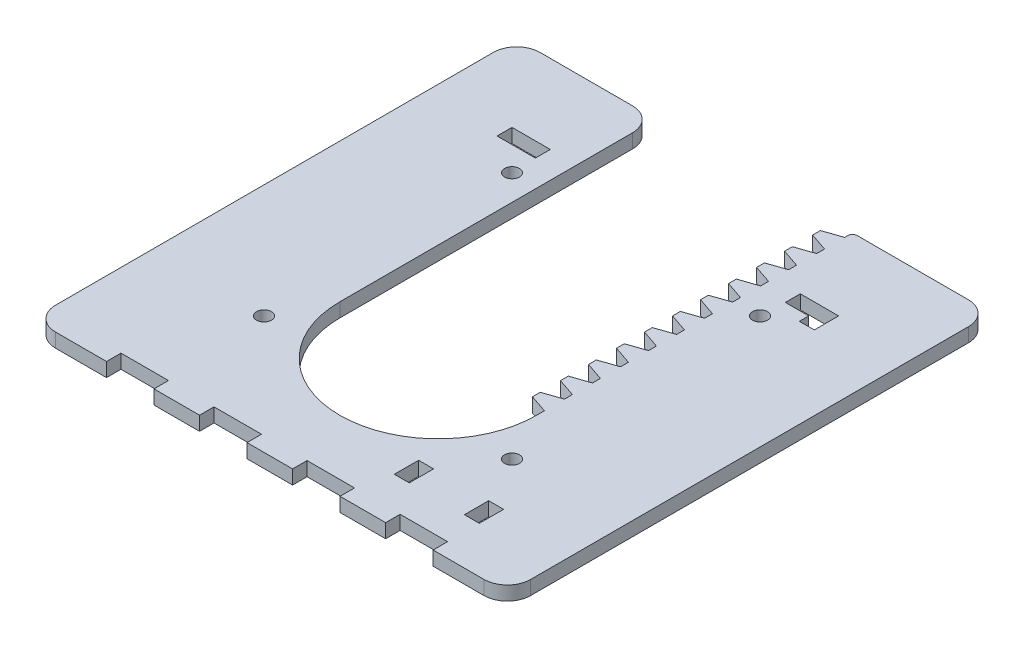
SolidWorks part; units mm, degrees
ref_plane "Front Plane" through (0, 0, 0) normal (0, 0, 1) x (1, 0, 0)
ref_plane "Top Plane" through (0, 0, 0) normal (0, 1, 0) x (1, 0, 0)
ref_plane "Right Plane" through (0, 0, 0) normal (1, 0, 0) x (0, 0, -1)
sketch "Sketch1" plane through (0, 0, 0) normal (0, 1, 0) x (1, 0, 0)
  line L0 (0, 0) -> (0, 21) construction
  line L1 (17.1887, 0) -> (0, 0) construction
  line L2 (21.0585, 3.843) -> (17.1887, 5.1665) construction
  line L3 (17.1887, 5.1665) -> (17.1887, 6.8335) construction
  line L4 (17.1887, 6.8335) -> (21.0585, 8.157) construction
  line L5 (21.0585, 9.843) -> (21.0585, 8.157) construction
  line L6 (21.0585, 9.843) -> (17.1887, 11.1665) construction
  line L7 (17.1887, 11.1665) -> (17.1887, 12.8335) construction
  line L8 (17.1887, 12.8335) -> (21.0585, 14.157) construction
  line L9 (21.0585, 15.843) -> (21.0585, 14.157) construction
  line L10 (21.0585, 15.843) -> (17.1887, 17.1665) construction
  line L11 (17.1887, 17.1665) -> (17.1887, 18.8335) construction
  line L12 (17.1887, 18.8335) -> (21.0585, 20.157) construction
  line L13 (21.0585, 21.843) -> (21.0585, 20.157) construction
  line L14 (21.0585, 21.843) -> (17.1887, 23.1665) construction
  line L15 (17.1887, 23.1665) -> (17.1887, 24.8335) construction
  line L16 (17.1887, 24.8335) -> (21.0585, 26.157) construction
  line L17 (21.0585, 27.843) -> (21.0585, 26.157) construction
  line L18 (21.0585, 27.843) -> (17.1887, 29.1665) construction
  line L19 (17.1887, 29.1665) -> (17.1887, 30.8335) construction
  line L20 (17.1887, 30.8335) -> (21.0585, 32.157) construction
  line L21 (21.0585, 33.843) -> (21.0585, 32.157) construction
  line L22 (21.0585, 33.843) -> (17.1887, 35.1665) construction
  line L23 (17.1887, 35.1665) -> (17.1887, 36.8335) construction
  line L24 (17.1887, 36.8335) -> (21.0585, 38.157) construction
  line L25 (21.0585, 39.843) -> (21.0585, 38.157) construction
  line L26 (21.0585, 39.843) -> (17.1887, 41.1665) construction
  line L27 (17.1887, 41.1665) -> (17.1887, 42.8335) construction
  line L28 (17.1887, 42.8335) -> (21.0585, 44.157) construction
  line L29 (21.0585, 45.843) -> (21.0585, 44.157) construction
  line L30 (21.0585, 45.843) -> (17.1887, 47.1665) construction
  line L31 (17.1887, 47.1665) -> (17.1887, 48.8335) construction
  line L32 (17.1887, 48.8335) -> (21.0585, 50.157) construction
  line L33 (21.0585, 51.843) -> (21.0585, 50.157) construction
  line L34 (21.0585, 51.843) -> (17.1887, 53.1665) construction
  line L35 (17.1887, 53.1665) -> (17.1887, 54.8335) construction
  line L36 (17.1887, 54.8335) -> (21.0585, 56.157) construction
  line L37 (21.0585, 57.843) -> (21.0585, 56.157) construction
  line L38 (21.0585, 57.843) -> (17.1887, 59.1665) construction
  line L39 (17.1887, 59.1665) -> (17.1887, 60.8335) construction
  line L40 (17.1887, 60.8335) -> (21.0585, 62.157) construction
  line L41 (21.0585, 62.157) -> (21.0585, 62.843) construction
  line L42 (45.8722, 63.843) -> (22.0585, 63.843) construction
  line L43 (50.8722, -34.9014) -> (50.8722, 58.843) construction
  line L44 (45.8722, -39.9014) -> (-45.8722, -39.9014) construction
  line L45 (-50.8722, 58.843) -> (-50.8722, -34.9014) construction
  line L46 (-45.8722, 63.843) -> (-22.0585, 63.843) construction
  line L47 (-21.0585, -3.843) -> (-21.0585, 62.843) construction
  line L48 (21.0585, -2.157) -> (21.0585, -3.843) construction
  line L49 (21.0585, -2.157) -> (17.1887, -0.8335) construction
  line L50 (17.1887, -0.8335) -> (17.1887, 0.8335) construction
  line L51 (17.1887, 0.8335) -> (21.0585, 2.157) construction
  line L52 (21.0585, 3.843) -> (21.0585, 2.157) construction
  line L53 (21.0585, 3.843) -> (17.1887, 5.1665)
  line L54 (17.1887, 5.1665) -> (17.1887, 6.8335)
  line L55 (17.1887, 6.8335) -> (21.0585, 8.157)
  line L56 (21.0585, 9.843) -> (21.0585, 8.157)
  line L57 (21.0585, 9.843) -> (17.1887, 11.1665)
  line L58 (17.1887, 11.1665) -> (17.1887, 12.8335)
  line L59 (17.1887, 12.8335) -> (21.0585, 14.157)
  line L60 (21.0585, 15.843) -> (21.0585, 14.157)
  line L61 (21.0585, 15.843) -> (17.1887, 17.1665)
  line L62 (17.1887, 17.1665) -> (17.1887, 18.8335)
  line L63 (17.1887, 18.8335) -> (21.0585, 20.157)
  line L64 (21.0585, 21.843) -> (21.0585, 20.157)
  line L65 (21.0585, 21.843) -> (17.1887, 23.1665)
  line L66 (17.1887, 23.1665) -> (17.1887, 24.8335)
  line L67 (17.1887, 24.8335) -> (21.0585, 26.157)
  line L68 (21.0585, 27.843) -> (21.0585, 26.157)
  line L69 (21.0585, 27.843) -> (17.1887, 29.1665)
  line L70 (17.1887, 29.1665) -> (17.1887, 30.8335)
  line L71 (17.1887, 30.8335) -> (21.0585, 32.157)
  line L72 (21.0585, 33.843) -> (21.0585, 32.157)
  line L73 (21.0585, 33.843) -> (17.1887, 35.1665)
  line L74 (17.1887, 35.1665) -> (17.1887, 36.8335)
  line L75 (17.1887, 36.8335) -> (21.0585, 38.157)
  line L76 (21.0585, 39.843) -> (21.0585, 38.157)
  line L77 (21.0585, 39.843) -> (17.1887, 41.1665)
  line L78 (17.1887, 41.1665) -> (17.1887, 42.8335)
  line L79 (17.1887, 42.8335) -> (21.0585, 44.157)
  line L80 (21.0585, 45.843) -> (21.0585, 44.157)
  line L81 (21.0585, 45.843) -> (17.1887, 47.1665)
  line L82 (17.1887, 47.1665) -> (17.1887, 48.8335)
  line L83 (17.1887, 48.8335) -> (21.0585, 50.157)
  line L84 (21.0585, 51.843) -> (21.0585, 50.157)
  line L85 (21.0585, 51.843) -> (17.1887, 53.1665)
  line L86 (17.1887, 53.1665) -> (17.1887, 54.8335)
  line L87 (17.1887, 54.8335) -> (21.0585, 56.157)
  line L88 (21.0585, 57.843) -> (21.0585, 56.157)
  line L89 (21.0585, 57.843) -> (17.1887, 59.1665)
  line L90 (17.1887, 59.1665) -> (17.1887, 60.8335)
  line L91 (17.1887, 60.8335) -> (21.0585, 62.157)
  line L92 (21.0585, 62.157) -> (21.0585, 62.843)
  line L93 (45.8722, 63.843) -> (22.0585, 63.843)
  line L94 (50.8722, -34.9014) -> (50.8722, 58.843)
  line L95 (45.8722, -39.9014) -> (-45.8722, -39.9014)
  line L96 (-50.8722, 58.843) -> (-50.8722, -34.9014)
  line L97 (-45.8722, 63.843) -> (-26.0585, 63.843)
  line L98 (-21.0585, -3.843) -> (-21.0585, 58.843)
  line L99 (21.0585, -2.157) -> (21.0585, -3.843)
  line L100 (21.0585, -2.157) -> (17.1887, -0.8335)
  line L101 (17.1887, -0.8335) -> (17.1887, 0.8335)
  line L102 (17.1887, 0.8335) -> (21.0585, 2.157)
  line L103 (21.0585, 3.843) -> (21.0585, 2.157)
  line L104 (0, 63.843) -> (0, -39.9014) construction
  line L105 (-51.8722, 11.9708) -> (51.8722, 11.9708) construction
  line L106 (0, 11.9708) -> (-51.8722, -39.9014) construction
  line L107 (51.8722, -24.9014) -> (-51.8722, -24.9014) construction
  line L108 (-36.8722, -39.9014) -> (-36.8722, 63.843) construction
  line L109 (36.8722, -39.9014) -> (36.8722, 63.843) construction
  line L110 (45.8722, -39.9014) -> (51.8722, -39.9014) construction
  line L111 (51.8722, -39.9014) -> (51.8722, 63.843) construction
  line L112 (51.8722, 63.843) -> (-51.8722, 63.843) construction
  line L113 (17.1887, 60) -> (0, 60) construction
  line L114 (-51.8722, 63.843) -> (-51.8722, -39.9014) construction
  line L115 (-51.8722, -39.9014) -> (-45.8722, -39.9014) construction
  circle A0 centre (0, 0) radius 21 construction
  circle A1 centre (0, 60) radius 21 construction
  arc A2 (22.0585, 63.843) -> (21.0585, 62.843) centre (22.0585, 62.843) ccw construction
  arc A3 (50.8722, 58.843) -> (45.8722, 63.843) centre (45.8722, 58.843) ccw construction
  arc A4 (45.8722, -39.9014) -> (50.8722, -34.9014) centre (45.8722, -34.9014) ccw construction
  arc A5 (-50.8722, -34.9014) -> (-45.8722, -39.9014) centre (-45.8722, -34.9014) ccw construction
  arc A6 (-45.8722, 63.843) -> (-50.8722, 58.843) centre (-45.8722, 58.843) ccw construction
  arc A8 (-21.0585, -3.843) -> (21.0585, -3.843) centre (0, -3.843) ccw construction
  arc A9 (22.0585, 63.843) -> (21.0585, 62.843) centre (22.0585, 62.843) ccw
  arc A10 (50.8722, 58.843) -> (45.8722, 63.843) centre (45.8722, 58.843) ccw
  arc A11 (45.8722, -39.9014) -> (50.8722, -34.9014) centre (45.8722, -34.9014) ccw
  arc A12 (-50.8722, -34.9014) -> (-45.8722, -39.9014) centre (-45.8722, -34.9014) ccw
  arc A13 (-45.8722, 63.843) -> (-50.8722, 58.843) centre (-45.8722, 58.843) ccw
  arc A14 (-21.0585, 58.843) -> (-26.0585, 63.843) centre (-26.0585, 58.843) ccw
  arc A15 (-21.0585, -3.843) -> (21.0585, -3.843) centre (0, -3.843) ccw
  circle A16 centre (26.5585, -14.5877) radius 1.6 construction
  circle A17 centre (-26.5585, -14.5877) radius 1.6 construction
  circle A18 centre (-26.5585, 38.5292) radius 1.6 construction
  circle A19 centre (26.5585, 38.5292) radius 1.6 construction
  circle A20 centre (26.5585, -14.5877) radius 1.6
  circle A21 centre (-26.5585, -14.5877) radius 1.6
  circle A22 centre (-26.5585, 38.5292) radius 1.6
  circle A23 centre (26.5585, 38.5292) radius 1.6
  circle A24 centre (0, 60) radius 21 construction
sketch "Sketch2" plane through (0, 0, 0) normal (0, 0, 1) x (1, 0, 0)
  line L0 (0, 0) -> (0, 3) construction
  line L1 (-50.8722, 0) -> (50.8722, 0)
  line L2 (-50.8722, 0) -> (-50.8722, 3)
  line L3 (-50.8722, 3) -> (50.8722, 3)
  line L4 (50.8722, 0) -> (50.8722, 3)
  line L5 (-50.8722, 3) -> (-51.8722, 3) construction
  line L6 (-51.8722, 3) -> (-51.8722, 3.75) construction
  line L7 (-51.8722, 3.75) -> (51.8722, 3.75) construction
  line L8 (51.8722, 3.75) -> (51.8722, 3) construction
  line L9 (51.8722, 3) -> (50.8722, 3) construction
  line L10 (50.8722, 0) -> (51.8722, 0) construction
  line L11 (51.8722, 0) -> (51.8722, -0.75) construction
  line L12 (51.8722, -0.75) -> (-51.8722, -0.75) construction
  line L13 (-51.8722, -0.75) -> (-51.8722, 0) construction
  line L14 (-51.8722, 0) -> (-50.8722, 0) construction
  line L15 (59.7, 47.7) -> (59.7, 44.7) construction
  dimension "D2" = 0.75
extrude "Boss-Extrude1" add sketch "Sketch1" along normal up to vertex (3 mm away) up to point (-50.8722, 3, 0)
ref_plane "edge" through (0, 0, -63.843) normal (0, 0, 1) x (1, 0, 0)
sketch "Sketch4" plane through (0, 0, 0) normal (0, 1, 0) x (1, 0, 0)
  line L12 (-25.0418, -23.0877) -> (-25.0418, -20.0877) construction
  line L13 (-15.0251, -23.0877) -> (-15.0251, -20.0877) construction
  line L14 (-5.0084, -23.0877) -> (-5.0084, -20.0877) construction
  line L15 (5.0084, -23.0877) -> (5.0084, -20.0877) construction
  line L16 (15.0251, -23.0877) -> (15.0251, -20.0877) construction
  line L17 (25.0418, -20.0877) -> (25.0418, -23.0877) construction
  line L18 (32.0585, -20.0877) -> (35.0585, -20.0877) construction
  line L30 (-25.0418, -23.0877) -> (-25.0418, -20.0877)
  line L31 (-15.0251, -23.0877) -> (-15.0251, -20.0877)
  line L32 (-5.0084, -23.0877) -> (-5.0084, -20.0877)
  line L33 (5.0084, -23.0877) -> (5.0084, -20.0877)
  line L34 (15.0251, -23.0877) -> (15.0251, -20.0877)
  line L35 (25.0418, -20.0877) -> (25.0418, -23.0877)
  line L36 (-35.0585, 47.0292) -> (35.0585, 47.0292) construction
  line L37 (-32.0585, 44.0292) -> (32.0585, 44.0292) construction
  line L38 (-32.0585, -20.0877) -> (-32.0585, 44.0292) construction
  line L39 (-35.0585, -23.0877) -> (-35.0585, 47.0292) construction
  line L40 (-32.0585, -20.0877) -> (32.0585, -20.0877) construction
  line L41 (-35.0585, -23.0877) -> (35.0585, -23.0877) construction
  line L42 (32.0585, -20.0877) -> (32.0585, 44.0292) construction
  line L43 (35.0585, -23.0877) -> (35.0585, 47.0292) construction
  line L44 (-35.0585, 47.0292) -> (35.0585, 47.0292)
  line L45 (-32.0585, 44.0292) -> (32.0585, 44.0292)
  line L46 (-32.0585, -20.0877) -> (-32.0585, 44.0292)
  line L47 (-35.0585, -23.0877) -> (-35.0585, 47.0292)
  line L48 (-32.0585, -20.0877) -> (32.0585, -20.0877)
  line L49 (-35.0585, -23.0877) -> (35.0585, -23.0877)
  line L50 (32.0585, -20.0877) -> (32.0585, 44.0292)
  line L51 (35.0585, -23.0877) -> (35.0585, 47.0292)
  line L52 (-23.0585, 44.0292) -> (-23.0585, 47.0292) construction
  line L53 (-23.0585, 44.0292) -> (-23.0585, 47.0292)
  line L54 (23.0585, 44.0292) -> (23.0585, 47.0292) construction
  line L55 (23.0585, 44.0292) -> (23.0585, 47.0292)
  line L56 (-32.0585, 44.0292) -> (-35.0585, 44.0292) construction
  line L57 (-25.0418, 47.0292) -> (-25.0418, 44.0292) construction
  line L58 (25.0418, 47.0292) -> (25.0418, 44.0292) construction
  line L59 (32.0585, 47.0292) -> (32.0585, 44.0292) construction
  line L66 (-32.0585, -20.0877) -> (-32.0585, -23.0877) construction
sketch "Sketch3" plane through (0, 0, 0) normal (0, 1, 0) x (1, 0, 0)
  line L0 (32.0585, 37.0125) -> (35.0585, 37.0125) construction
  line L1 (25.0418, 47.0292) -> (25.0418, 44.0292) construction
  line L2 (25.0418, 44.0292) -> (32.0585, 44.0292) construction
  line L3 (32.0585, 44.0292) -> (32.0585, 37.0125) construction
  line L4 (32.0585, 37.0125) -> (35.0585, 37.0125) construction
  line L5 (35.0585, 37.0125) -> (35.0585, 47.0292) construction
  line L6 (35.0585, 47.0292) -> (25.0418, 47.0292) construction
  line L7 (35.0585, -23.0877) -> (35.0585, 47.0292) construction
  line L8 (32.0585, 11.9708) -> (0, 11.9708) construction
  line L9 (0, 11.9708) -> (0, 44.0292) construction
  line L10 (32.0585, 11.9708) -> (0, 11.9708) construction
  line L11 (0, 11.9708) -> (0, 44.0292) construction
  line L13 (35.0585, 26.9958) -> (32.0585, 26.9958) construction
  line L14 (35.0585, 16.9791) -> (32.0585, 16.9791) construction
  line L15 (32.0585, -20.0877) -> (32.0585, 44.0292) construction
  line L16 (35.0585, 26.9958) -> (32.0585, 26.9958) construction
  line L17 (35.0585, 26.9958) -> (35.0585, 16.9791) construction
  line L18 (35.0585, 16.9791) -> (32.0585, 16.9791) construction
  line L19 (32.0585, 26.9958) -> (32.0585, 16.9791) construction
  line L20 (35.1585, 27.0958) -> (35.1585, 16.8791)
  line L21 (35.1585, 16.8791) -> (31.9585, 16.8791)
  line L22 (31.9585, 27.0958) -> (31.9585, 16.8791)
  line L23 (35.1585, 27.0958) -> (31.9585, 27.0958)
  line L24 (35.1585, 36.9125) -> (35.1585, 47.1292)
  line L25 (35.1585, 47.1292) -> (24.9418, 47.1292)
  line L26 (24.9418, 47.1292) -> (24.9418, 43.9292)
  line L27 (24.9418, 43.9292) -> (31.9585, 43.9292)
  line L28 (31.9585, 43.9292) -> (31.9585, 36.9125)
  line L29 (31.9585, 36.9125) -> (35.1585, 36.9125)
  line L30 (35.1585, -3.1543) -> (31.9585, -3.1543)
  line L31 (31.9585, -3.1543) -> (31.9585, 7.0624)
  line L32 (35.1585, 7.0624) -> (31.9585, 7.0624)
  line L33 (35.1585, -3.1543) -> (35.1585, 7.0624)
  line L34 (31.9585, -19.9877) -> (31.9585, -12.971)
  line L35 (24.9418, -19.9877) -> (31.9585, -19.9877)
  line L36 (24.9418, -23.1877) -> (24.9418, -19.9877)
  line L37 (35.1585, -23.1877) -> (24.9418, -23.1877)
  line L38 (35.1585, -12.971) -> (35.1585, -23.1877)
  line L39 (31.9585, -12.971) -> (35.1585, -12.971)
  line L40 (-31.9585, 43.9292) -> (-31.9585, 36.9125)
  line L41 (-24.9418, 43.9292) -> (-31.9585, 43.9292)
  line L42 (-24.9418, 47.1292) -> (-24.9418, 43.9292)
  line L43 (-35.1585, 47.1292) -> (-24.9418, 47.1292)
  line L44 (-35.1585, 36.9125) -> (-35.1585, 47.1292)
  line L45 (-31.9585, 36.9125) -> (-35.1585, 36.9125)
  line L46 (-35.1585, 27.0958) -> (-35.1585, 16.8791)
  line L47 (-35.1585, 16.8791) -> (-31.9585, 16.8791)
  line L48 (-31.9585, 27.0958) -> (-31.9585, 16.8791)
  line L49 (-35.1585, 27.0958) -> (-31.9585, 27.0958)
  line L50 (-35.1585, -3.1543) -> (-31.9585, -3.1543)
  line L51 (-31.9585, -3.1543) -> (-31.9585, 7.0624)
  line L52 (-35.1585, 7.0624) -> (-31.9585, 7.0624)
  line L53 (-35.1585, -3.1543) -> (-35.1585, 7.0624)
  line L54 (-35.1585, -12.971) -> (-35.1585, -23.1877)
  line L55 (-31.9585, -12.971) -> (-35.1585, -12.971)
  line L56 (-31.9585, -19.9877) -> (-31.9585, -12.971)
  line L57 (-24.9418, -19.9877) -> (-31.9585, -19.9877)
  line L58 (-24.9418, -23.1877) -> (-24.9418, -19.9877)
  line L59 (-35.1585, -23.1877) -> (-24.9418, -23.1877)
  dimension "D1" = 0.1
extrude "Cut-Extrude1" [suppressed] cut sketch "Sketch3" along normal through all
sketch "Sketch6" plane through (0, 0, 0) normal (0, 1, 0) x (1, 0, 0)
  line L0 (34.8722, -39.9014) -> (34.8722, 63.843) construction
  line L1 (31.8722, -39.9014) -> (31.8722, 63.843) construction
  line L2 (24.9087, -39.9014) -> (24.9087, 63.843) construction
  line L3 (-24.9087, -39.9014) -> (-24.9087, 63.843) construction
  line L4 (14.9452, -39.9014) -> (14.9452, -36.9014)
  line L5 (14.9452, -36.9014) -> (4.9817, -36.9014)
  line L6 (4.9817, -36.9014) -> (4.9817, -39.9014)
  line L7 (4.9817, -39.9014) -> (14.9452, -39.9014)
  line L8 (14.9452, -39.9014) -> (14.9452, -36.9014) construction
  line L9 (14.9452, -36.9014) -> (4.9817, -36.9014) construction
  line L10 (4.9817, -36.9014) -> (4.9817, -39.9014) construction
  line L11 (4.9817, -39.9014) -> (14.9452, -39.9014) construction
  line L12 (34.8722, -36.9014) -> (24.9087, -36.9014)
  line L13 (34.8722, -39.9014) -> (34.8722, -36.9014)
  line L14 (24.9087, -39.9014) -> (34.8722, -39.9014)
  line L15 (24.9087, -36.9014) -> (24.9087, -39.9014)
  line L16 (34.8722, -36.9014) -> (24.9087, -36.9014) construction
  line L17 (34.8722, -39.9014) -> (34.8722, -36.9014) construction
  line L18 (24.9087, -39.9014) -> (34.8722, -39.9014) construction
  line L19 (24.9087, -36.9014) -> (24.9087, -39.9014) construction
  line L20 (-24.9087, -36.9014) -> (-34.8722, -36.9014)
  line L21 (-24.9087, -39.9014) -> (-24.9087, -36.9014)
  line L22 (-34.8722, -39.9014) -> (-24.9087, -39.9014)
  line L23 (-34.8722, -36.9014) -> (-34.8722, -39.9014)
  line L24 (-24.9087, -36.9014) -> (-34.8722, -36.9014) construction
  line L25 (-24.9087, -39.9014) -> (-24.9087, -36.9014) construction
  line L26 (16.8722, -39.9014) -> (16.8722, 63.843) construction
  line L27 (-34.8722, -39.9014) -> (-24.9087, -39.9014) construction
  line L28 (51.8722, 63.843) -> (51.8722, -39.9014) construction
  line L29 (-34.8722, -36.9014) -> (-34.8722, -39.9014) construction
  line L30 (-14.9452, -39.9014) -> (-4.9817, -39.9014)
  line L31 (-14.9452, -36.9014) -> (-14.9452, -39.9014)
  line L32 (-4.9817, -36.9014) -> (-14.9452, -36.9014)
  line L33 (51.8722, -39.9014) -> (-51.8722, -39.9014) construction
  line L34 (51.8722, 63.843) -> (-51.8722, 63.843) construction
  line L35 (-51.8722, 63.843) -> (-51.8722, -39.9014) construction
  line L36 (51.8722, 63.843) -> (51.8722, -39.9014) construction
  line L37 (51.8722, -39.9014) -> (-51.8722, -39.9014) construction
  line L38 (51.8722, 63.843) -> (-51.8722, 63.843) construction
  line L39 (-51.8722, 63.843) -> (-51.8722, -39.9014) construction
  line L40 (-4.9817, -39.9014) -> (-4.9817, -36.9014)
  line L41 (-14.9452, -39.9014) -> (-4.9817, -39.9014) construction
  line L42 (-14.9452, -36.9014) -> (-14.9452, -39.9014) construction
  line L43 (-4.9817, -36.9014) -> (-14.9452, -36.9014) construction
  line L44 (-4.9817, -39.9014) -> (-4.9817, -36.9014) construction
  line L45 (-34.8722, 43.843) -> (-26.8722, 43.843)
  line L46 (-34.8722, 46.843) -> (-34.8722, 43.843)
  line L47 (-26.8722, 46.843) -> (-34.8722, 46.843)
  line L48 (-26.8722, 43.843) -> (-26.8722, 46.843)
  line L49 (-34.8722, 43.843) -> (-26.8722, 43.843) construction
  line L50 (-34.8722, 46.843) -> (-34.8722, 43.843) construction
  line L51 (-26.8722, 46.843) -> (-34.8722, 46.843) construction
  line L52 (-26.8722, 43.843) -> (-26.8722, 46.843) construction
  line L53 (34.8722, -24.9014) -> (31.8722, -24.9014)
  line L54 (34.8722, -29.9014) -> (34.8722, -24.9014)
  line L55 (31.8722, -29.9014) -> (34.8722, -29.9014)
  line L56 (31.8722, -24.9014) -> (31.8722, -29.9014)
  line L57 (34.8722, -24.9014) -> (31.8722, -24.9014) construction
  line L58 (34.8722, -29.9014) -> (34.8722, -24.9014) construction
  line L59 (31.8722, -29.9014) -> (34.8722, -29.9014) construction
  line L60 (31.8722, -24.9014) -> (31.8722, -29.9014) construction
  line L61 (-34.8722, -39.9014) -> (-34.8722, 63.843) construction
  line L62 (-51.8722, 43.843) -> (51.8722, 43.843) construction
  line L63 (34.8722, 41.843) -> (34.8722, 46.843)
  line L64 (34.8722, 46.843) -> (26.8722, 46.843)
  line L65 (26.8722, 46.843) -> (26.8722, 43.843)
  line L66 (26.8722, 43.843) -> (31.8722, 43.843)
  line L67 (31.8722, 43.843) -> (31.8722, 41.843)
  line L68 (31.8722, 41.843) -> (34.8722, 41.843)
  line L69 (34.8722, 41.843) -> (34.8722, 46.843) construction
  line L70 (34.8722, 46.843) -> (26.8722, 46.843) construction
  line L71 (26.8722, 46.843) -> (26.8722, 43.843) construction
  line L72 (26.8722, 43.843) -> (31.8722, 43.843) construction
  line L73 (31.8722, 43.843) -> (31.8722, 41.843) construction
  line L74 (31.8722, 41.843) -> (34.8722, 41.843) construction
  line L75 (51.8722, 46.843) -> (-51.8722, 46.843) construction
  line L76 (51.8722, -24.9014) -> (-51.8722, -24.9014) construction
  line L77 (51.8722, -36.9014) -> (-51.8722, -36.9014) construction
  line L78 (34.8722, -39.9014) -> (34.8722, 63.843) construction
  line L79 (31.8722, -39.9014) -> (31.8722, 63.843) construction
  line L80 (24.9087, -39.9014) -> (24.9087, 63.843) construction
  line L81 (-24.9087, -39.9014) -> (-24.9087, 63.843) construction
  line L82 (-34.8722, -39.9014) -> (-34.8722, 63.843) construction
  line L83 (-51.8722, 43.843) -> (51.8722, 43.843) construction
  line L84 (51.8722, 46.843) -> (-51.8722, 46.843) construction
  line L85 (51.8722, -24.9014) -> (-51.8722, -24.9014) construction
  line L86 (51.8722, -36.9014) -> (-51.8722, -36.9014) construction
  line L87 (15.0452, -40.0014) -> (15.0452, -36.8014)
  line L88 (15.0452, -36.8014) -> (4.8817, -36.8014)
  line L89 (4.8817, -36.8014) -> (4.8817, -40.0014)
  line L90 (4.8817, -40.0014) -> (15.0452, -40.0014)
  line L91 (34.9722, -36.8014) -> (24.8087, -36.8014)
  line L92 (24.8087, -36.8014) -> (24.8087, -40.0014)
  line L93 (24.8087, -40.0014) -> (34.9722, -40.0014)
  line L94 (34.9722, -40.0014) -> (34.9722, -36.8014)
  line L95 (-24.8087, -36.8014) -> (-34.9722, -36.8014)
  line L96 (-34.9722, -36.8014) -> (-34.9722, -40.0014)
  line L97 (-34.9722, -40.0014) -> (-24.8087, -40.0014)
  line L98 (-24.8087, -40.0014) -> (-24.8087, -36.8014)
  line L99 (-15.0452, -40.0014) -> (-4.8817, -40.0014)
  line L100 (-4.8817, -40.0014) -> (-4.8817, -36.8014)
  line L101 (-4.8817, -36.8014) -> (-15.0452, -36.8014)
  line L102 (-15.0452, -36.8014) -> (-15.0452, -40.0014)
  line L103 (-34.9722, 43.743) -> (-26.7722, 43.743)
  line L104 (-26.7722, 43.743) -> (-26.7722, 46.943)
  line L105 (-26.7722, 46.943) -> (-34.9722, 46.943)
  line L106 (-34.9722, 46.943) -> (-34.9722, 43.743)
  line L107 (34.9722, -24.8014) -> (31.7722, -24.8014)
  line L108 (31.7722, -24.8014) -> (31.7722, -30.0014)
  line L109 (31.7722, -30.0014) -> (34.9722, -30.0014)
  line L110 (34.9722, -30.0014) -> (34.9722, -24.8014)
  line L111 (34.9722, 41.743) -> (34.9722, 46.943)
  line L112 (34.9722, 46.943) -> (26.7722, 46.943)
  line L113 (26.7722, 46.943) -> (26.7722, 43.743)
  line L114 (26.7722, 43.743) -> (31.7722, 43.743)
  line L115 (31.7722, 43.743) -> (31.7722, 41.743)
  line L116 (31.7722, 41.743) -> (34.9722, 41.743)
  line L117 (19.8722, 63.843) -> (19.8722, -39.9014) construction
  line L118 (19.9722, -24.8014) -> (16.7722, -24.8014)
  line L119 (19.8722, -24.9014) -> (16.8722, -24.9014) construction
  line L120 (19.8722, -24.9014) -> (19.8722, -29.9014) construction
  line L121 (19.8722, -29.9014) -> (16.8722, -29.9014) construction
  line L122 (16.8722, -24.9014) -> (16.8722, -29.9014) construction
  line L123 (16.7722, -24.8014) -> (16.7722, -30.0014)
  line L124 (19.9722, -30.0014) -> (16.7722, -30.0014)
  line L125 (19.9722, -24.8014) -> (19.9722, -30.0014)
  dimension "D1" = 0
  dimension "D2" = 0
  dimension "D3" = 0
  dimension "D4" = 0
  dimension "D5" = 0
  dimension "D6" = 0
  dimension "D7" = 0
  dimension "D8" = 0.1
  dimension "D9" = 0.1
extrude "Cut-Extrude4" cut sketch "Sketch6" along normal through all
